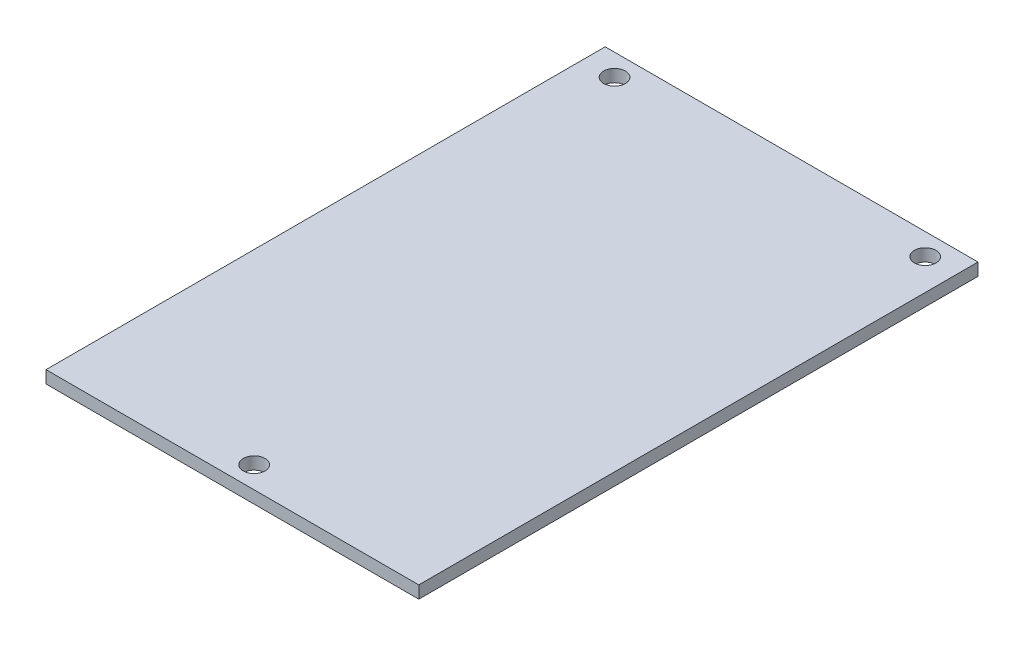
SolidWorks part; units mm, degrees
ref_plane "Front" through (0, 0, 0) normal (0, 0, 1) x (1, 0, 0)
ref_plane "Top" through (0, 0, 0) normal (0, 1, 0) x (1, 0, 0)
ref_plane "Right" through (0, 0, 0) normal (1, 0, 0) x (0, 0, -1)
sketch "Sketch1" plane through (0, 0, 0) normal (0, 1, 0) x (1, 0, 0)
  line L1 (-30, 45) -> (30, 45)
  line L2 (-30, 45) -> (-30, -45)
  line L3 (-30, -45) -> (30, -45)
  line L4 (30, 45) -> (30, -45)
  line L5 (-30, 45) -> (30, -45) construction
  line L6 (-30, -45) -> (30, 45) construction
  point P0 (0, 0)
  dimension "D1" = 60
  dimension "D2" = 90
extrude "Boss-Extrude1" add sketch "Sketch1" along normal blind 2
sketch "Sketch2" plane through (0, 2, 0) normal (0, 1, 0) x (1, 0, 0)
  line L0 (-30, 41.5) -> (30, 41.5) construction
  line L1 (-30, 45) -> (-30, -45) construction
  line L2 (30, -45) -> (30, 45) construction
  line L3 (0, 45) -> (0, -45) construction
  line L4 (30, 45) -> (-30, 45) construction
  line L5 (-30, -45) -> (30, -45) construction
  circle A0 centre (-25, 41.5) radius 1.75
  circle A1 centre (25, 41.5) radius 1.75
  circle A2 centre (0, -41.5) radius 1.75
  dimension "D1" = 3.5
  dimension "D2" = 3.5
  dimension "D3" = 5
  dimension "D4" = 3.5
extrude "Cut-Extrude1" cut sketch "Sketch2" against normal through all
